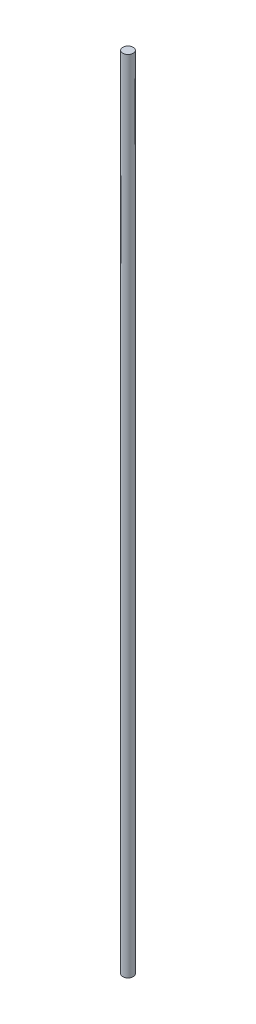
SolidWorks part; units mm, degrees
ref_plane "Alzado" through (0, 0, 0) normal (0, 0, 1) x (1, 0, 0)
ref_plane "Planta" through (0, 0, 0) normal (0, 1, 0) x (1, 0, 0)
ref_plane "Vista lateral" through (0, 0, 0) normal (1, 0, 0) x (0, 0, -1)
sketch "Croquis1" plane through (0, 0, 0) normal (0, 1, 0) x (1, 0, 0)
  circle A0 centre (0, 0) radius 6.35
  dimension "D1" = 12.7
sketch "Croquis2" plane through (0, 0, 0) normal (0, 0, 1) x (1, 0, 0)
  line L0 (0, 0) -> (0, 980)
  dimension "D1" = 980
sweep "Barrer1" add profiles "Croquis1" path "Croquis2"
